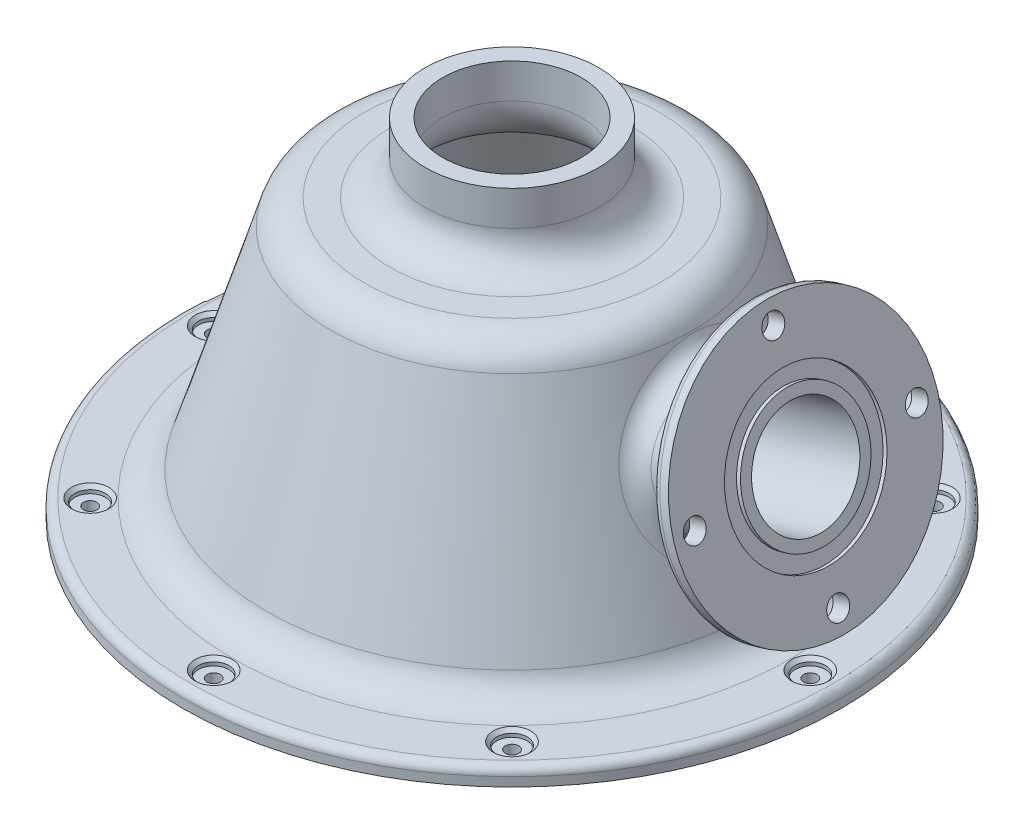
SolidWorks part; units mm, degrees
ref_plane "Front Plane" through (0, 0, 0) normal (0, 0, 1) x (1, 0, 0)
ref_plane "Top Plane" through (0, 0, 0) normal (0, 1, 0) x (1, 0, 0)
ref_plane "Right Plane" through (0, 0, 0) normal (1, 0, 0) x (0, 0, -1)
sketch "Sketch1" plane through (0, 0, 0) normal (0, 0, 1) x (1, 0, 0)
  line L0 (0, 0) -> (0, 76.015) construction
  line L1 (-60.325, 0) -> (-60.325, 3.175)
  line L2 (-60.325, 3.175) -> (-51.0092, 3.175)
  line L3 (-44.9366, 7.6684) -> (-33.1238, 46.3066)
  line L4 (-27.0512, 50.8) -> (-22.225, 50.8)
  line L5 (-15.875, 57.15) -> (-15.875, 63.5)
  line L6 (-15.875, 63.5) -> (-12.7, 63.5)
  line L7 (-60.325, 0) -> (-51.0092, 0)
  line L9 (-41.9004, 6.7402) -> (-30.0875, 45.3783)
  line L10 (-27.0512, 47.625) -> (-22.225, 47.625)
  line L11 (-12.7, 57.15) -> (-12.7, 63.5)
  arc A0 (-51.0092, 3.175) -> (-44.9366, 7.6684) centre (-51.0092, 9.525) ccw
  arc A1 (-22.225, 50.8) -> (-15.875, 57.15) centre (-22.225, 57.15) ccw
  arc A2 (-33.1238, 46.3066) -> (-27.0512, 50.8) centre (-27.0512, 44.45) cw
  arc A3 (-51.0092, 0) -> (-41.9004, 6.7402) centre (-51.0092, 9.525) ccw
  arc A4 (-30.0875, 45.3783) -> (-27.0512, 47.625) centre (-27.0512, 44.45) cw
  arc A5 (-22.225, 47.625) -> (-12.7, 57.15) centre (-22.225, 57.15) ccw
  point P16 (-31.75, 50.8)
  dimension "D1" = 6.35
  dimension "D2" = 17
  dimension "D3" = 50.8
  dimension "D4" = 3.175
  dimension "D5" = 63.5
  dimension "D6" = 63.5
  dimension "D7" = 31.75
  dimension "D8" = 120.65
revolve "Revolve1" add sketch "Sketch1" angle 360 about L0
fillet "Fillet1" radius 1.524 1 edges at (0, 3.175, -60.325)
hole_wizard "CBORE for #2 Binding Head Machine Screw1" positions "Sketch3" profile "Sketch2" counterbore size "#2" standard "ANSI Inch" end condition through all
sketch "Sketch3" plane through (0, 3.175, 0) normal (0, 1, 0) x (1, 0, 0)
  point P0 (0, 54.61)
  dimension "D1" = 54.61
sketch "Sketch2" plane through (0, 3.175, -54.61) normal (1, 0, 0) x (0, 0, 1)
  line L0 (0, 0) -> (0, 3.175)
  line L1 (0, 3.175) -> (1.2192, 3.175)
  line L3 (1.2192, 3.175) -> (1.2192, 1.27)
  line L4 (2.7788, 1.27) -> (1.2192, 1.27)
  line L5 (2.7788, 1.27) -> (2.7788, 0.635)
  line L6 (2.7788, 0.635) -> (3.4138, 0)
  line L7 (3.4138, 0) -> (0, 0)
  line L8 (-2.7788, 0.635) -> (-3.4138, 0) construction
  line L11 (0, -6.35) -> (0, 107.95) construction
  dimension "Thru Hole Dia." = 2.4384
  dimension "Thru Hole Depth" = 3.175
  dimension "C'Bore Dia." = 5.5575
  dimension "C'Bore Depth" = 1.27
  dimension "Near C'Sink Dia." = 6.8275
  dimension "Near C'Sink Angle" = 90
pattern_circular "CirPattern1" count 8 over 360 about axis through (0, 0, 0) along (0, 1, 0) of "CBORE for #2 Binding Head Machine Screw1"
sketch "Sketch5" plane through (0, 0, 0) normal (0, 0, 1) x (1, 0, 0)
  line L0 (0, 18.5887) -> (0, 0) construction
  line L1 (0, 18.5887) -> (53.7785, 35.0305) construction
  line L2 (44.9366, 7.6684) -> (33.1238, 46.3066) construction
  line L3 (31.6305, 41.5394) -> (43.9928, 45.319)
  line L5 (46.1008, 49.2835) -> (43.6873, 57.1778)
  line L6 (43.6873, 57.1778) -> (46.7236, 58.1061)
  line L7 (46.7236, 58.1061) -> (53.7785, 35.0305)
  line L8 (53.7785, 35.0305) -> (35.3437, 29.3944)
  line L9 (35.3437, 29.3944) -> (31.6305, 41.5394)
  arc A0 (43.9928, 45.319) -> (46.1008, 49.2835) centre (43.0646, 48.3552) ccw
  dimension "D3" = 3.175
  dimension "D1" = 2.8218
  dimension "D2" = 3.175
  dimension "D4" = 25.4
  dimension "D5" = 48.26
revolve "Revolve2" add sketch "Sketch5" angle 360 about L1
fillet "Fillet2" radius 3.81 1 edges at (34.6855, 35.406, 11.2245)
fillet "Fillet3" radius 1.524 1 edges at (57.7972, 11.0266, 0)
sketch "Sketch6" plane through (58.9758, 18.0307, 0) normal (0.9563, 0.2924, 0) x (0, 0, -1)
  circle A0 centre (0, 17.7765) radius 9.525
  dimension "D1" = 19.05
extrude "Cut-Extrude1" cut sketch "Sketch6" against normal up to surface (19.6304 mm away)
sketch "Sketch9" plane through (58.9758, 18.0307, 0) normal (0.9563, 0.2924, 0) x (0, 0, -1)
  line L0 (0, 0) -> (0, 17.7202) construction
sketch "Sketch10" plane through (58.9758, 18.0307, 0) normal (0.9563, 0.2924, 0) x (0, 0, -1)
  circle A0 centre (0, 17.7765) radius 11.4681
  circle A1 centre (0, 17.7765) radius 14.2875
  dimension "D1" = 28.575
  dimension "D2" = 22.9362
extrude "Cut-Extrude2" cut sketch "Sketch10" against normal blind 0.762
hole_wizard "#10-32 Tapped Hole1" positions "Sketch15" profile "Sketch14" tap size "#10-32" standard "ANSI Inch"
sketch "Sketch15" plane through (58.9758, 18.0307, 0) normal (0.9563, 0.2924, 0) x (0, 0, -1)
  circle A0 centre (0, 17.7765) radius 20.32 construction
  circle A1 centre (0, 17.7765) radius 24.13 construction
  point P4 (0, 38.0965)
  point P6 (20.32, 17.7765)
  point P8 (0, -2.5435)
  point P10 (-20.32, 17.7765)
  dimension "D1" = 3.81
sketch "Sketch14" plane through (53.7785, 35.0305, 20.32) normal (0, 0, 1) x (-0.2924, 0.9563, 0)
  line L0 (0, 0) -> (0, 13.2529)
  line L1 (0, 13.2529) -> (2.0193, 12.0396)
  line L2 (2.0193, 12.0396) -> (2.0193, 0)
  line L5 (2.0193, 0) -> (0, 0)
  line L10 (0, 13.2529) -> (-2.0193, 12.0396) construction
  line L11 (0, -6.35) -> (0, 107.95) construction
  dimension "Tap Drill Dia." = 4.0386
  dimension "Tap Drill Depth" = 12.0396
  dimension "Drill Angle" = 118
